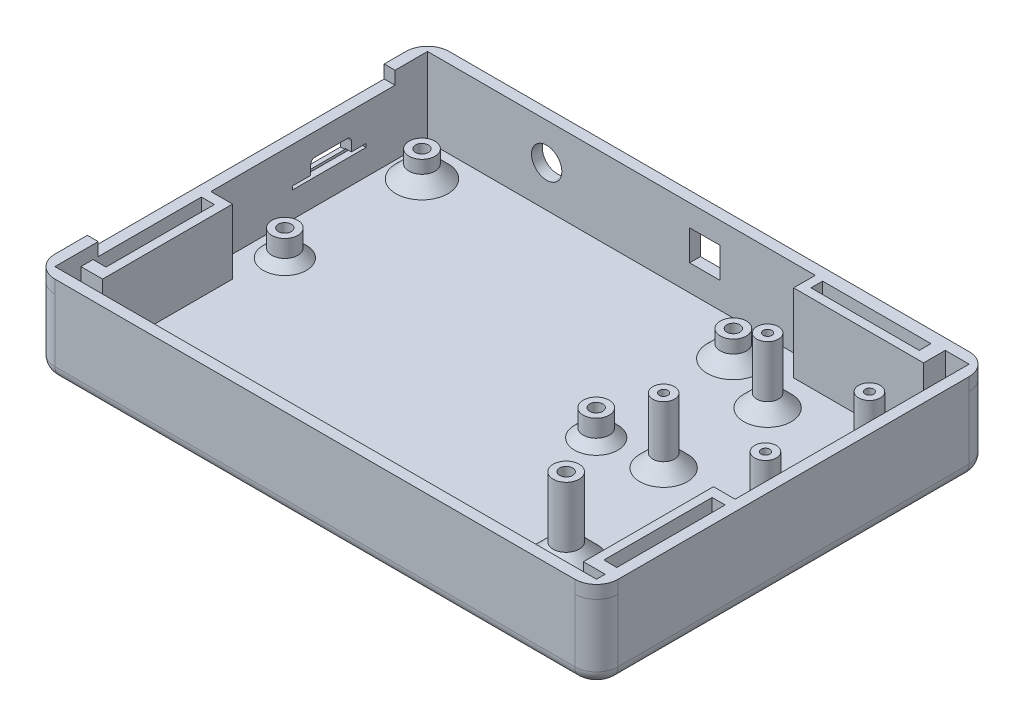
SolidWorks part; units mm, degrees
ref_plane "Front Plane" through (0, 0, 0) normal (0, 0, 1) x (1, 0, 0)
ref_plane "Top Plane" through (0, 0, 0) normal (0, 1, 0) x (1, 0, 0)
ref_plane "Right Plane" through (0, 0, 0) normal (1, 0, 0) x (0, 0, -1)
sketch "Sketch2" plane through (0, 0, 0) normal (0, 1, 0) x (1, 0, 0)
  line L1 (0, 0) -> (130, 0)
  line L2 (0, 0) -> (0, -91)
  line L3 (0, -91) -> (130, -91)
  line L4 (130, 0) -> (130, -91)
  dimension "D1" = 130
  dimension "D2" = 91
extrude "Boss-Extrude1" add sketch "Sketch2" along normal blind 2.5
sketch "Sketch3" plane through (0, 2.5, 0) normal (0, 1, 0) x (1, 0, 0)
  line L0 (0, -91) -> (130, -91) construction
  line L1 (0, 0) -> (2.5, 0)
  line L2 (0, 0) -> (0, -91)
  line L3 (0, -91) -> (2.5, -91)
  line L4 (2.5, 0) -> (2.5, -91)
  line L6 (130, 0) -> (127.5, 0)
  line L7 (130, 0) -> (130, -91)
  line L8 (130, -91) -> (127.5, -91)
  line L9 (127.5, 0) -> (127.5, -91)
  line L10 (2.5, 0) -> (127.5, 0)
  line L11 (2.5, 0) -> (2.5, -2.5)
  line L12 (2.5, -2.5) -> (127.5, -2.5)
  line L13 (127.5, 0) -> (127.5, -2.5)
  line L14 (2.5, -91) -> (127.5, -91)
  line L15 (2.5, -91) -> (2.5, -88.5)
  line L16 (2.5, -88.5) -> (127.5, -88.5)
  line L17 (127.5, -91) -> (127.5, -88.5)
  line M18 (0, 0) -> (0, -91)
  line M19 (0, -91) -> (130, -91)
  line M20 (130, -91) -> (130, 0)
  line M21 (130, 0) -> (0, 0)
  dimension "D1" = 2.5
  dimension "D2" = 2.5
  dimension "D3" = 2.5
  dimension "D4" = 2.5
extrude "Boss-Extrude2" add sketch "Sketch3" along normal blind 15 contours L9 M21 M19 M20 | L4 L12 L9 M21 | L16 L4 L9 M19 | L4 M21 M18 M19
sketch "Sketch13" plane through (0, 2.5, 0) normal (0, 1, 0) x (1, 0, 0)
  line L0 (2.5, -88.5) -> (127.5, -88.5) construction
  line L1 (7.5, -88.5) -> (84.7, -88.5)
  line L2 (7.5, -88.5) -> (7.5, -47.5)
  line L3 (7.5, -47.5) -> (84.7, -47.5)
  line L4 (84.7, -88.5) -> (84.7, -47.5)
  line L5 (2.5, -2.5) -> (2.5, -88.5) construction
  dimension "D1" = 5
  dimension "D2" = 77.2
  dimension "D3" = 41
sketch "Sketch14" plane through (2.5, 0, 0) normal (1, 0, 0) x (0, 0, -1)
  line L0 (-2.5, 17.5) -> (-2.5, 2.5) construction
  line L1 (-29.48, 12.35) -> (-20.08, 12.35)
  line L2 (-29.48, 12.35) -> (-29.48, 8.95)
  line L3 (-29.48, 8.95) -> (-20.08, 8.95)
  line L4 (-20.08, 12.35) -> (-20.08, 8.95)
  line L5 (-2.5, 2.5) -> (-88.5, 2.5) construction
  dimension "D1" = 9.4
  dimension "D2" = 3.4
  dimension "D3" = 17.58
  dimension "D4" = 6.45
extrude "Cut-Extrude1" cut sketch "Sketch14" against normal blind 10
fillet "Fillet3" radius 1 1 edges at (1.25, 12.35, 20.08)
fillet "Fillet4" radius 1 1 edges at (1.25, 12.35, 29.48)
sketch "Sketch17" plane through (2.5, 0, 0) normal (1, 0, 0) x (0, 0, -1)
  line L1 (-33.68, 9.2) -> (-16.68, 9.2)
  line L2 (-33.68, 9.2) -> (-33.68, 8.4)
  line L3 (-33.68, 8.4) -> (-16.68, 8.4)
  line L4 (-16.68, 9.2) -> (-16.68, 8.4)
  line L5 (-29.48, 8.95) -> (-20.08, 8.95) construction
  dimension "D1" = 17
  dimension "D2" = 0.8
  dimension "D3" = 3.4
  dimension "D4" = 0.25
extrude "Cut-Extrude3" cut sketch "Sketch17" against normal blind 1.5
sketch "Sketch19" plane through (0, 2.5, 0) normal (0, 1, 0) x (1, 0, 0)
  line L0 (2.5, -2.5) -> (127.5, -2.5) construction
  line L1 (2.5, -2.5) -> (2.5, -88.5) construction
  circle A0 centre (9.3, -10.58) radius 3
  dimension "D1" = 6
  dimension "D2" = 8.08
  dimension "D3" = 6.8
extrude "Boss-Extrude3" add sketch "Sketch19" along normal blind 6
sketch "Sketch20" plane through (0, 8.5, 0) normal (0, 1, 0) x (1, 0, 0)
  circle A0 centre (9.3, -10.58) radius 1.5
  circle A1 centre (9.3, -10.58) radius 3 construction
  dimension "D1" = 3
extrude "Cut-Extrude4" cut sketch "Sketch20" against normal blind 5
sketch "Sketch21" plane through (0, 2.5, 0) normal (0, 1, 0) x (1, 0, 0)
  line L0 (2.5, -2.5) -> (127.5, -2.5) construction
  line L1 (2.5, -2.5) -> (2.5, -88.5) construction
  circle A0 centre (9.3, -42.23) radius 3
  dimension "D1" = 6
  dimension "D2" = 39.73
  dimension "D3" = 6.8
extrude "Boss-Extrude4" add sketch "Sketch21" along normal blind 6
sketch "Sketch22" plane through (0, 8.5, 0) normal (0, 1, 0) x (1, 0, 0)
  circle A0 centre (9.3, -42.23) radius 1.5
  circle A1 centre (9.3, -42.23) radius 3 construction
  dimension "D1" = 3
extrude "Cut-Extrude5" cut sketch "Sketch22" against normal blind 5
sketch "Sketch23" plane through (0, 2.5, 0) normal (0, 1, 0) x (1, 0, 0)
  line L0 (2.5, -2.5) -> (2.5, -88.5) construction
  line L1 (2.5, -2.5) -> (127.5, -2.5) construction
  circle A0 centre (81.17, -10.58) radius 3
  dimension "D1" = 6
  dimension "D2" = 78.67
  dimension "D3" = 8.08
extrude "Boss-Extrude5" add sketch "Sketch23" along normal blind 6 contours A0
sketch "Sketch24" plane through (0, 8.5, 0) normal (0, 1, 0) x (1, 0, 0)
  circle A0 centre (81.17, -10.58) radius 1.5
  circle A1 centre (81.17, -10.58) radius 3 construction
  dimension "D1" = 3
extrude "Cut-Extrude6" cut sketch "Sketch24" against normal blind 5
sketch "Sketch25" plane through (0, 2.5, 0) normal (0, 1, 0) x (1, 0, 0)
  line L0 (2.5, -2.5) -> (127.5, -2.5) construction
  line L1 (2.5, -2.5) -> (2.5, -88.5) construction
  circle A0 centre (81.17, -42.23) radius 3
  dimension "D1" = 6
  dimension "D2" = 39.73
  dimension "D3" = 78.67
extrude "Boss-Extrude6" add sketch "Sketch25" along normal blind 6
sketch "Sketch26" plane through (0, 8.5, 0) normal (0, 1, 0) x (1, 0, 0)
  circle A0 centre (81.17, -42.23) radius 1.5
  circle A1 centre (81.17, -42.23) radius 3 construction
  dimension "D1" = 3
extrude "Cut-Extrude7" cut sketch "Sketch26" against normal blind 5
fillet "Fillet5" radius 5 4 edges at (0, 8.75, 0) (130, 8.75, 0) (130, 8.75, 91) (0, 8.75, 91)
sketch "Sketch28" plane through (0, 2.5, 0) normal (0, 1, 0) x (1, 0, 0)
  line L0 (2.5, -2.5) -> (127.5, -2.5) construction
  line L1 (127.5, -2.5) -> (127.5, -88.5) construction
  circle A0 centre (118.5, -16.5) radius 2.5
  dimension "D1" = 14
  dimension "D2" = 9
  dimension "D3" = 5
extrude "Boss-Extrude7" add sketch "Sketch28" along normal blind 15 contours A0
sketch "Sketch29" plane through (0, 2.5, 0) normal (0, 1, 0) x (1, 0, 0)
  line L0 (127.5, -2.5) -> (127.5, -88.5) construction
  line L1 (2.5, -2.5) -> (127.5, -2.5) construction
  circle A0 centre (118.5, -40.5) radius 2.5
  dimension "D1" = 5
  dimension "D2" = 9
  dimension "D3" = 38
extrude "Boss-Extrude8" add sketch "Sketch29" along normal blind 15
sketch "Sketch30" plane through (0, 17.5, 0) normal (0, 1, 0) x (1, 0, 0)
  circle A0 centre (118.5, -16.5) radius 1
  circle A1 centre (118.5, -16.5) radius 2.5 construction
  dimension "D1" = 2
extrude "Cut-Extrude8" cut sketch "Sketch30" against normal blind 6
sketch "Sketch31" plane through (0, 17.5, 0) normal (0, 1, 0) x (1, 0, 0)
  circle A0 centre (118.5, -40.5) radius 1
  circle A1 centre (118.5, -40.5) radius 2.5 construction
  dimension "D1" = 2
extrude "Cut-Extrude9" cut sketch "Sketch31" against normal blind 6
sketch "Sketch33" plane through (0, 2.5, 0) normal (0, 1, 0) x (1, 0, 0)
  line L0 (2.5, -2.5) -> (127.5, -2.5) construction
  circle A0 centre (95, -16.5) radius 2.5
  circle A1 centre (118.5, -16.5) radius 2.5 construction
  dimension "D1" = 5
  dimension "D2" = 14
  dimension "D3" = 23.5
extrude "Boss-Extrude9" add sketch "Sketch33" along normal blind 15
sketch "Sketch34" plane through (0, 2.5, 0) normal (0, 1, 0) x (1, 0, 0)
  line L0 (2.5, -2.5) -> (127.5, -2.5) construction
  circle A0 centre (95, -40.5) radius 2.5
  circle A1 centre (118.5, -40.5) radius 2.5 construction
  dimension "D1" = 5
  dimension "D2" = 38
  dimension "D3" = 23.5
extrude "Boss-Extrude10" add sketch "Sketch34" along normal blind 15
sketch "Sketch35" plane through (0, 17.5, 0) normal (0, 1, 0) x (1, 0, 0)
  circle A0 centre (95, -16.5) radius 1
  dimension "D1" = 2
extrude "Cut-Extrude10" cut sketch "Sketch35" against normal blind 6
sketch "Sketch36" plane through (0, 17.5, 0) normal (0, 1, 0) x (1, 0, 0)
  circle A0 centre (95, -40.5) radius 1
  dimension "D1" = 2
extrude "Cut-Extrude11" cut sketch "Sketch36" against normal blind 6
sketch "Sketch39" plane through (0, 17.5, 0) normal (0, 1, 0) x (1, 0, 0)
  line L0 (2.5, -88.5) -> (127.5, -88.5) construction
  line L1 (0, -88.5) -> (130, -88.5)
  line L2 (0, -88.5) -> (0, -91)
  line L3 (0, -91) -> (130, -91)
  line L4 (130, -88.5) -> (130, -91)
  line L6 (0, -5) -> (0, -86) construction
  point P6 (0, -89.75)
  dimension "D1" = 130
  dimension "D2" = 2.5
  dimension "D3" = 0
extrude "Boss-Extrude11" add sketch "Sketch39" along normal blind 3
sketch "Sketch40" plane through (0, 17.5, 0) normal (0, 1, 0) x (1, 0, 0)
  line L0 (130, -91) -> (130, -88.5) construction
  line L1 (127.5, 0) -> (130, 0)
  line L2 (127.5, 0) -> (127.5, -91)
  line L3 (127.5, -91) -> (130, -91)
  line L4 (130, 0) -> (130, -91)
  line L5 (130, -86) -> (130, -5) construction
  line L9 (0, -91) -> (130, -91) construction
  dimension "D1" = 2.5
  dimension "D2" = 91
  dimension "D3" = 0
extrude "Boss-Extrude12" add sketch "Sketch40" along normal blind 3
fillet "Fillet10" radius 5 1 edges at (130, 19, 91)
sketch "Sketch41" plane through (0, 17.5, 0) normal (0, 1, 0) x (1, 0, 0)
  line L0 (2.5, -2.5) -> (127.5, -2.5) construction
  line L1 (0, -2.5) -> (130, -2.5)
  line L2 (0, -2.5) -> (0, 0)
  line L3 (0, 0) -> (130, 0)
  line L4 (130, -2.5) -> (130, 0)
  line L5 (0, -5) -> (0, -86) construction
  dimension "D1" = 130
  dimension "D2" = 2.5
  dimension "D3" = 0
extrude "Boss-Extrude13" add sketch "Sketch41" along normal blind 3
fillet "Fillet11" radius 5 1 edges at (130, 19, 0)
sketch "Sketch43" plane through (0, 17.5, 0) normal (0, 1, 0) x (1, 0, 0)
  line L0 (125, 0) -> (0, 0) construction
  line L1 (0, 0) -> (2.5, 0)
  line L2 (0, 0) -> (0, -10)
  line L3 (0, -10) -> (2.5, -10)
  line L4 (2.5, 0) -> (2.5, -10)
  line L5 (2.5, -2.5) -> (2.5, -88.5) construction
  dimension "D1" = 10
  dimension "D2" = 2.5
  dimension "D3" = 0
extrude "Boss-Extrude14" add sketch "Sketch43" along normal blind 3
fillet "Fillet12" radius 5 1 edges at (0, 19, 0)
sketch "Sketch45" plane through (0, 17.5, 0) normal (0, 1, 0) x (1, 0, 0)
  line L0 (7.5, -88.5) -> (84.7, -88.5) construction
  line L1 (2.5, -78.5) -> (0, -78.5)
  line L2 (2.5, -78.5) -> (2.5, -88.5)
  line L3 (2.5, -88.5) -> (0, -88.5)
  line L4 (0, -78.5) -> (0, -88.5)
  line L5 (0, -10) -> (0, -86) construction
  dimension "D1" = 10
  dimension "D2" = 2.5
  dimension "D3" = 0
extrude "Boss-Extrude15" add sketch "Sketch45" along normal blind 3
fillet "Fillet13" radius 5 1 edges at (0, 19, 91)
sketch "Sketch46" plane through (0, 2.5, 0) normal (0, 1, 0) x (1, 0, 0)
  line L0 (2.5, -2.5) -> (127.5, -2.5) construction
  line L1 (92, -2.5) -> (122, -2.5)
  line L2 (92, -2.5) -> (92, -7.5)
  line L3 (92, -7.5) -> (122, -7.5)
  line L4 (122, -2.5) -> (122, -7.5)
  line L5 (130, -86) -> (130, -5) construction
  dimension "D1" = 5
  dimension "D2" = 8
  dimension "D3" = 30
extrude "Boss-Extrude16" add sketch "Sketch46" along normal blind 18
sketch "Sketch47" plane through (0, 2.5, 0) normal (0, 1, 0) x (1, 0, 0)
  line L0 (127.5, -2.5) -> (127.5, -88.5) construction
  line L1 (122.5, -56.5) -> (127.5, -56.5)
  line L2 (122.5, -56.5) -> (122.5, -86.5)
  line L3 (122.5, -86.5) -> (127.5, -86.5)
  line L4 (127.5, -56.5) -> (127.5, -86.5)
  line L5 (2.5, -88.5) -> (127.5, -88.5) construction
  dimension "D1" = 5
  dimension "D2" = 30
  dimension "D3" = 2
extrude "Boss-Extrude17" add sketch "Sketch47" along normal blind 18
sketch "Sketch48" plane through (0, 2.5, 0) normal (0, 1, 0) x (1, 0, 0)
  line L0 (2.5, -2.5) -> (2.5, -88.5) construction
  line L1 (2.5, -52.5) -> (7.5, -52.5)
  line L2 (2.5, -52.5) -> (2.5, -82.5)
  line L3 (2.5, -82.5) -> (7.5, -82.5)
  line L4 (7.5, -52.5) -> (7.5, -82.5)
  line L5 (7.5, -88.5) -> (7.5, -47.5) construction
  line L6 (127.5, -88.5) -> (2.5, -88.5) construction
  dimension "D1" = 30
  dimension "D2" = 5
  dimension "D3" = 6
extrude "Boss-Extrude18" add sketch "Sketch48" along normal blind 15
sketch "Sketch49" plane through (0, 20.5, 0) normal (0, 1, 0) x (1, 0, 0)
  line L0 (92, -7.5) -> (122, -7.5) construction
  line L1 (94, -2.8022) -> (119, -2.8022)
  line L2 (94, -2.8022) -> (94, -5.5)
  line L3 (94, -5.5) -> (119, -5.5)
  line L4 (119, -2.8022) -> (119, -5.5)
  line L5 (92, -2.5) -> (92, -7.5) construction
  dimension "D1" = 2
  dimension "D2" = 25
  dimension "D3" = 2
extrude "Cut-Extrude12" cut sketch "Sketch49" against normal blind 10
sketch "Sketch50" plane through (0, 17.5, 0) normal (0, 1, 0) x (1, 0, 0)
  line L0 (7.5, -88.5) -> (7.5, -47.5) construction
  line L1 (2.5, -54.7) -> (5.5, -54.7)
  line L2 (2.5, -54.7) -> (2.5, -79.7)
  line L3 (2.5, -79.7) -> (5.5, -79.7)
  line L4 (5.5, -54.7) -> (5.5, -79.7)
  line L5 (7.5, -52.5) -> (2.5, -52.5) construction
  point P6 (4, -54.7)
  dimension "D1" = 25
  dimension "D2" = 3
  dimension "D3" = 2
  dimension "D4" = 2.2
extrude "Cut-Extrude13" cut sketch "Sketch50" against normal blind 10
sketch "Sketch51" plane through (0, 20.5, 0) normal (0, 1, 0) x (1, 0, 0)
  line L0 (122.5, -56.5) -> (122.5, -86.5) construction
  line L1 (124.5, -58.8) -> (127.5, -58.8)
  line L2 (124.5, -58.8) -> (124.5, -83.8)
  line L3 (124.5, -83.8) -> (127.5, -83.8)
  line L4 (127.5, -58.8) -> (127.5, -83.8)
  line L5 (122.5, -86.5) -> (127.5, -86.5) construction
  dimension "D1" = 25
  dimension "D2" = 3
  dimension "D3" = 2
  dimension "D4" = 2.7
extrude "Cut-Extrude14" cut sketch "Sketch51" against normal blind 10
sketch "Sketch52" plane through (0, 2.5, 0) normal (0, 1, 0) x (1, 0, 0)
  line L0 (2.5, -2.5) -> (92, -2.5) construction
  line L1 (2.5, -2.5) -> (2.5, -52.5) construction
  circle A0 centre (102.5, -70.5) radius 3
  dimension "D1" = 6
  dimension "D2" = 68
  dimension "D3" = 100
extrude "Boss-Extrude19" add sketch "Sketch52" along normal blind 18
sketch "Sketch53" plane through (0, 20.5, 0) normal (0, 1, 0) x (1, 0, 0)
  circle A0 centre (102.5, -70.5) radius 1.5
  circle A1 centre (102.5, -70.5) radius 3 construction
  dimension "D1" = 3
extrude "Cut-Extrude15" cut sketch "Sketch53" against normal blind 16
fillet "Fillet14" radius 3 8 edges at (1.4645, 0, 89.5355) (0, 0, 45.5) (1.4645, 0, 1.4645) (65, 0, 0) (128.5355, 0, 1.4645) (130, 0, 45.5) (128.5355, 0, 89.5355) (65, 0, 91)
chamfer "Chamfer2" distance 3 angle 45 1 edges at (9.3, 2.5, 13.58)
chamfer "Chamfer3" distance 2 angle 45 1 edges at (9.3, 2.5, 45.23)
chamfer "Chamfer4" distance 3 angle 45 1 edges at (81.17, 2.5, 13.58)
chamfer "Chamfer5" distance 3 angle 45 4 edges at (118.5, 2.5, 43) (118.5, 2.5, 19) (95, 2.5, 43) (95, 2.5, 19)
chamfer "Chamfer6" distance 4 angle 45 1 edges at (102.5, 2.5, 73.5)
chamfer "Chamfer7" distance 2 angle 45 1 edges at (81.17, 2.5, 45.23)
sketch "Sketch54" plane through (0, 0, 0) normal (0, 0, -1) x (-1, 0, 0)
  line L0 (-125, 20.5) -> (-5, 20.5) construction
  line L1 (-70, 15.5) -> (-63, 15.5)
  line L2 (-70, 15.5) -> (-70, 8.5)
  line L3 (-70, 8.5) -> (-63, 8.5)
  line L4 (-63, 15.5) -> (-63, 8.5)
  line L5 (-125, 17.5) -> (-125, 3) construction
  point P4 (-66.5, 15.5)
  dimension "D1" = 7
  dimension "D2" = 7
  dimension "D3" = 5
  dimension "D4" = 55
extrude "Cut-Extrude16" cut sketch "Sketch54" against normal mid plane 10
sketch "Sketch55" plane through (0, 0, 0) normal (0, 0, -1) x (-1, 0, 0)
  line L0 (-7.5, 2.5) -> (-84.7, 2.5) construction
  line L1 (-5, 3) -> (-5, 17.5) construction
  circle A0 centre (-30, 12) radius 3.5
  dimension "D1" = 7
  dimension "D2" = 9.5
  dimension "D3" = 25
extrude "Cut-Extrude17" cut sketch "Sketch55" against normal mid plane 10
